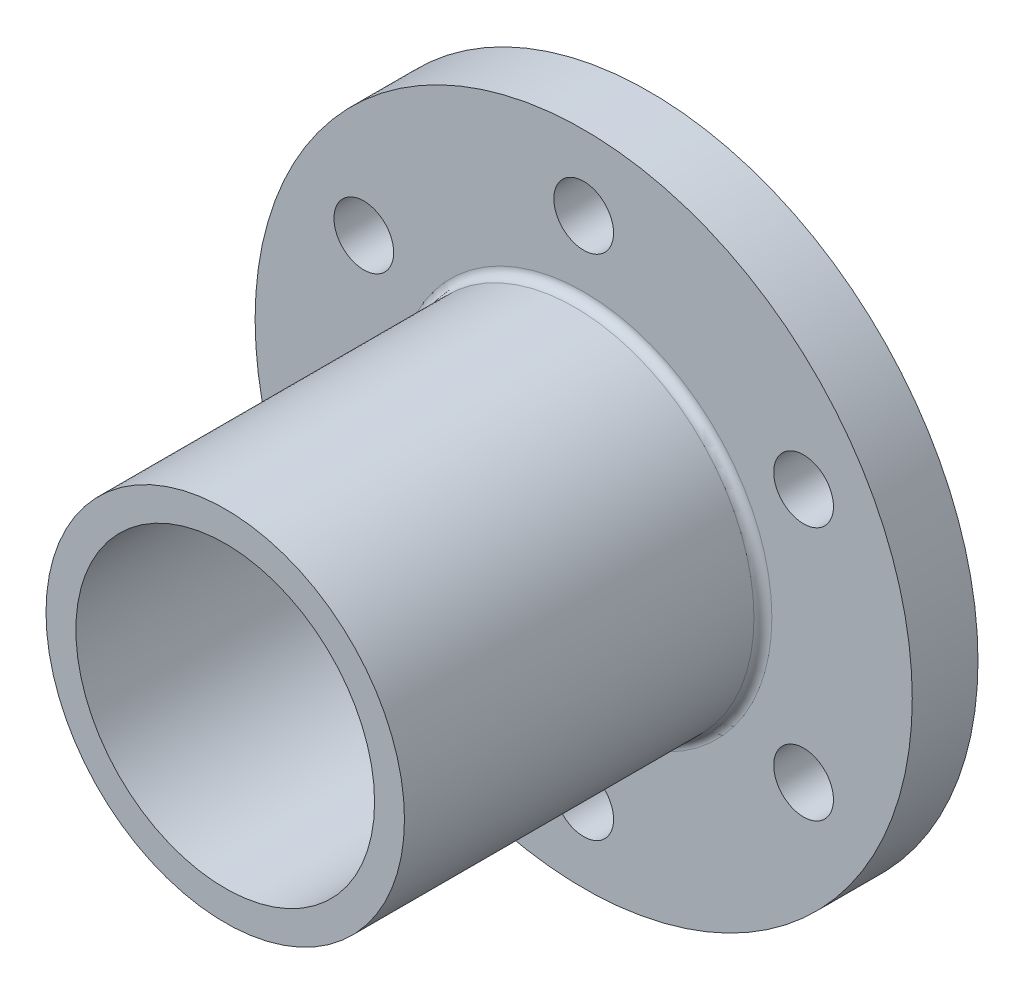
SolidWorks part; units mm, degrees
ref_plane "Front Plane" through (0, 0, 0) normal (0, 0, 1) x (1, 0, 0)
ref_plane "Top Plane" through (0, 0, 0) normal (0, 1, 0) x (1, 0, 0)
ref_plane "Right Plane" through (0, 0, 0) normal (1, 0, 0) x (0, 0, -1)
sketch "Sketch2" plane through (0, 0, 0) normal (0, 0, 1) x (1, 0, 0)
  circle A0 centre (0, 0) radius 110
  dimension "D1" = 220
extrude "Boss-Extrude1" add sketch "Sketch2" along normal blind 22
sketch "Sketch3" plane through (0, 0, 22) normal (0, 0, 1) x (1, 0, 0)
  circle A0 centre (0, 0) radius 60
  dimension "D1" = 120
extrude "Boss-Extrude2" add sketch "Sketch3" along normal blind 120
sketch "Sketch4" plane through (0, 0, 142) normal (0, 0, 1) x (1, 0, 0)
  circle A0 centre (0, 0) radius 50
  dimension "D1" = 100
extrude "Cut-Extrude1" cut sketch "Sketch4" against normal through all
sketch "Sketch5" plane through (0, 0, 22) normal (0, 0, 1) x (1, 0, 0)
  circle A0 centre (0, 85) radius 10
  circle A1 centre (73.6122, 42.5) radius 10
  circle A2 centre (73.6122, -42.5) radius 10
  circle A3 centre (0, -85) radius 10
  circle A4 centre (-73.6122, -42.5) radius 10
  circle A5 centre (-73.6122, 42.5) radius 10
  point P16 (0, 0)
  dimension "D1" = 20
  dimension "D2" = 85
  dimension "D3" = 6
extrude "Cut-Extrude2" cut sketch "Sketch5" against normal through all
fillet "Fillet1" radius 3 1 edges at (60, 0, 22)
